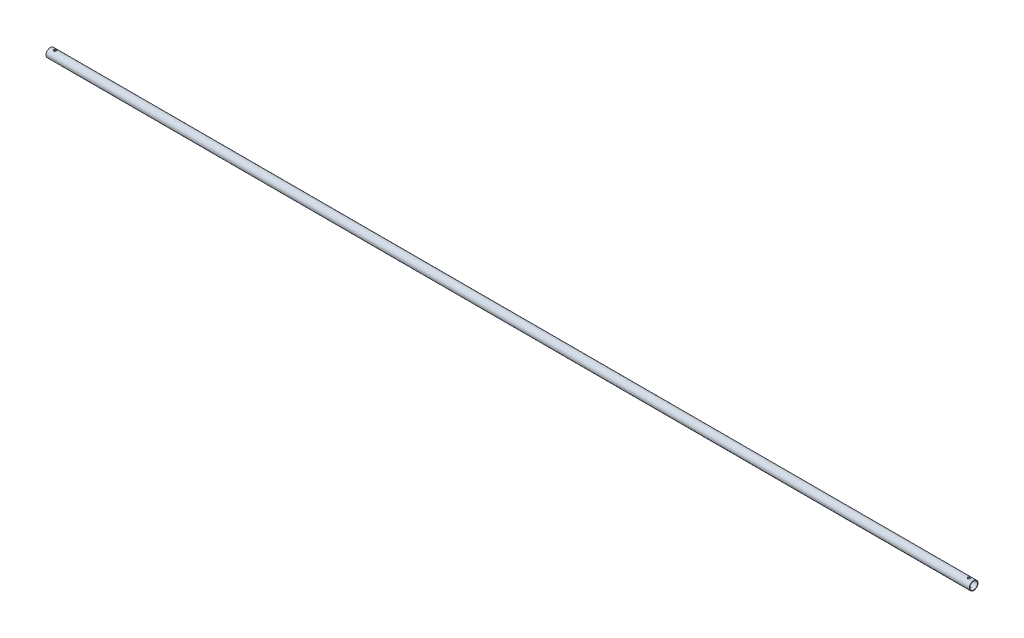
SolidWorks part; units mm, degrees
ref_plane "Front Plane" through (0, 0, 0) normal (0, 0, 1) x (1, 0, 0)
ref_plane "Top Plane" through (0, 0, 0) normal (0, 1, 0) x (1, 0, 0)
ref_plane "Right Plane" through (0, 0, 0) normal (1, 0, 0) x (0, 0, -1)
sketch "Sketch1" plane through (0, 0, 0) normal (1, 0, 0) x (0, 0, -1)
  circle A0 centre (0, 0) radius 11.7094
  circle A1 centre (0, 0) radius 10.4648
  dimension "D1" = 23.4188
  dimension "D2" = 20.9296
extrude "Boss-Extrude1" add sketch "Sketch1" along normal blind 2501.9
ref_plane "Plane1" through (1250.95, 0, 0) normal (-1, 0, 0) x (0, 0, 1)
sketch "Sketch2" plane through (0, 0, 0) normal (0, 1, 0) x (1, 0, 0)
  circle A0 centre (12.7, 0) radius 3.3782
  dimension "D1" = 6.7564
  dimension "D2" = 12.7
extrude "Cut-Extrude1" cut sketch "Sketch2" against normal through all both and the other way through all
mirror "Mirror1" about plane through (1250.95, 0, 0) normal (-1, 0, 0) of "Cut-Extrude1"
